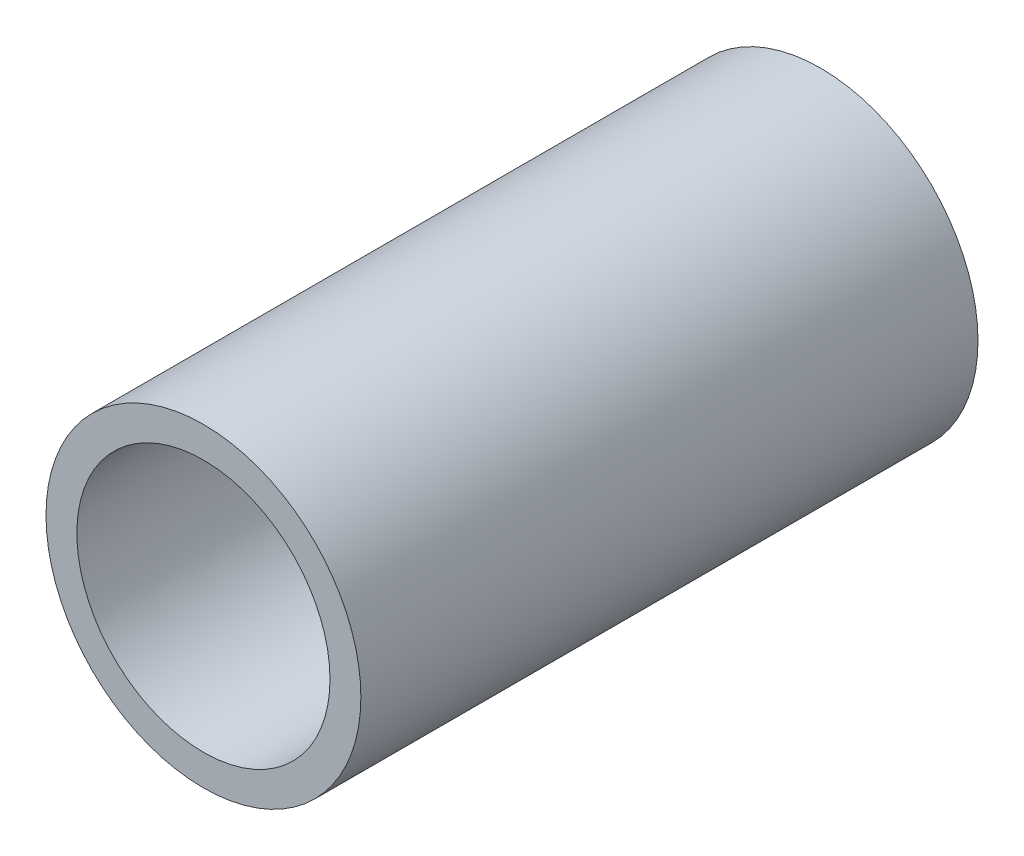
SolidWorks part; units mm, degrees
ref_plane "Front Plane" through (0, 0, 0) normal (0, 0, 1) x (1, 0, 0)
ref_plane "Top Plane" through (0, 0, 0) normal (0, 1, 0) x (1, 0, 0)
ref_plane "Right Plane" through (0, 0, 0) normal (1, 0, 0) x (0, 0, -1)
sketch "Sketch1" plane through (0, 0, 0) normal (0, 0, 1) x (1, 0, 0)
  line L0 (6.35, 0) -> (-6.35, 0) construction
  line L1 (0, -5.1054) -> (0, 5.1054) construction
  line L2 (0, -6.35) -> (0, 6.35) construction
  circle A0 centre (0, 0) radius 6.35 construction
  circle A1 centre (0, 0) radius 5.1054 construction
  point P6 (0, 0)
  point P7 (-5.1054, 0)
  point P8 (5.1054, 0)
  point P10 (-6.35, 0)
  point P11 (6.35, 0)
  point P14 (0, 0)
  point P17 (0, 0)
  point P18 (0, 5.1054)
  point P19 (0, 6.35)
  point P20 (0, -5.1054)
  point P21 (0, -6.35)
  dimension "OD" = 12.7
  dimension "ID" = 10.2108
  dimension "Wall Thickness" = 1.2446
sketch "Sketch2" plane through (0, 0, 0) normal (1, 0, 0) x (0, 0, -1)
  line L0 (0, -5.1054) -> (0, 5.1054) construction
  line L1 (0, -5.1054) -> (0, 5.1054) construction
  line L2 (0, -6.35) -> (0, 6.35) construction
  line L3 (0, -6.35) -> (0, 6.35) construction
  line L4 (12.446, 6.35) -> (-12.446, 6.35) construction
  line L5 (12.446, 5.1054) -> (-12.446, 5.1054) construction
  line L6 (12.446, -5.1054) -> (-12.446, -5.1054) construction
  line L7 (12.446, -6.35) -> (-12.446, -6.35) construction
  line L8 (-12.446, -6.35) -> (-12.446, 6.35) construction
  line L9 (12.446, 6.35) -> (12.446, -6.35) construction
  line L10 (12.446, 0) -> (-12.446, 0) construction
  line L11 (-6.8016, -6.35) -> (-6.8016, 6.35) construction
  line L12 (6.8016, -6.35) -> (6.8016, 6.35) construction
  point P7 (0, 6.35)
  point P10 (0, 5.1054)
  point P13 (0, -5.1054)
  point P16 (0, -6.35)
  point P17 (-12.446, -6.35)
  point P18 (-12.446, -5.1054)
  point P19 (-12.446, 5.1054)
  point P20 (-12.446, 6.35)
  point P21 (12.446, 6.35)
  point P22 (12.446, 5.1054)
  point P23 (12.446, -5.1054)
  point P24 (12.446, -6.35)
  point P28 (0, 0)
  point P30 (-6.8016, 0)
  point P31 (-6.8016, -6.35)
  point P32 (-6.8016, 6.35)
  point P35 (6.8016, 0)
  point P36 (6.8016, 6.35)
  point P37 (6.8016, -6.35)
  dimension "Length" = 24.892
  dimension "Break Line" = 5.6444
sketch "Sketch3" plane through (0, 0, 0) normal (0, 0, 1) x (1, 0, 0)
  circle A0 centre (0, 0) radius 5.1054 construction
  circle A1 centre (0, 0) radius 6.35 construction
  circle A2 centre (0, 0) radius 5.1054
  circle A3 centre (0, 0) radius 6.35
extrude "Boss-Extrude1" add sketch "Sketch3" along normal up to vertex (12.446 mm away) and the other way up to vertex (12.446 mm away) up to point (0, 0, 12.446) other way up to point (0, 0, -12.446)
equation "\"Break Line@Sketch2\"=\"OD@Sketch1\"/2.25"
